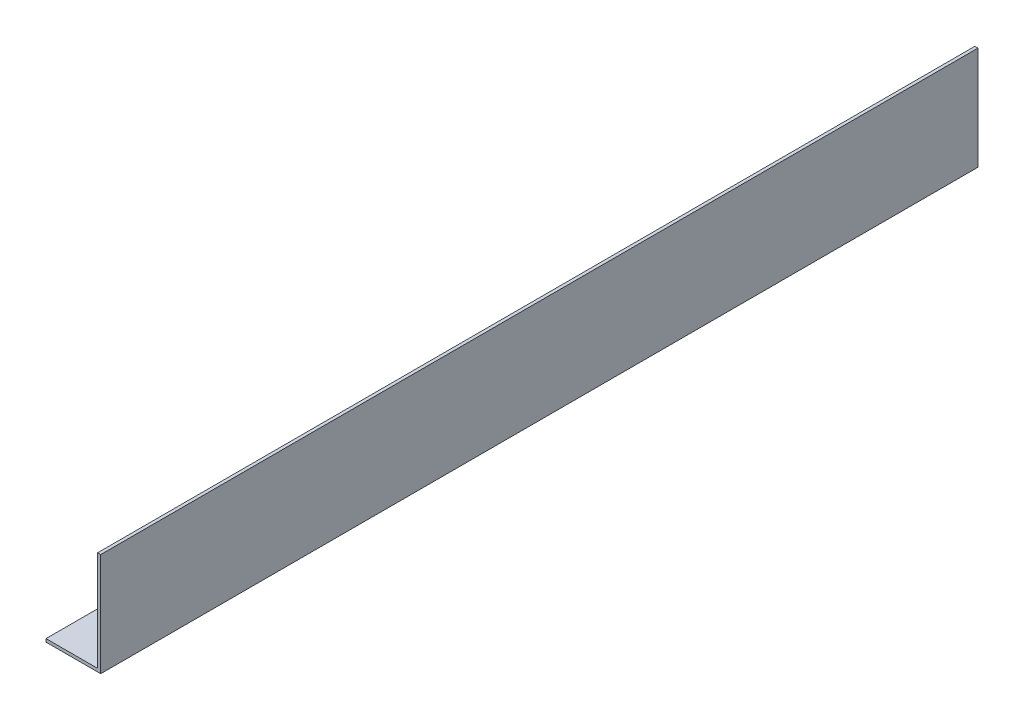
SolidWorks part; units mm, degrees
ref_plane "Front Plane" through (0, 0, 0) normal (0, 0, 1) x (1, 0, 0)
ref_plane "Top Plane" through (0, 0, 0) normal (0, 1, 0) x (1, 0, 0)
ref_plane "Right Plane" through (0, 0, 0) normal (1, 0, 0) x (0, 0, -1)
sketch "Sketch3" plane through (0, 0, 0) normal (0, 0, 1) x (1, 0, 0)
  line L11 (0, 0) -> (-26.924, 0)
  line L12 (0, 0) -> (0, 50.8)
  line L13 (0, 50.8) -> (-1.524, 50.8)
  line L14 (-1.524, 50.8) -> (-1.524, 1.524)
  line L15 (-1.524, 1.524) -> (-26.924, 1.524)
  line L16 (-26.924, 1.524) -> (-26.924, 0)
  dimension "D1" = 1.524
  dimension "D2" = 1.524
  dimension "D3" = 50.8
  dimension "D4" = 25.4
extrude "Boss-Extrude2" add sketch "Sketch3" along normal blind 431.8
sketch "Sketch4" plane through (0, 0, 0) normal (1, 0, 0) x (0, 0, -1)
  line L0 (-260.858, 26.162) -> (-384.048, 26.162) construction
  line L1 (-260.858, 11.557) -> (-384.048, 11.557)
  line L2 (-260.858, 40.767) -> (-384.048, 40.767)
  line L3 (-431.8, 0) -> (-431.8, 50.8) construction
  line L4 (-431.8, 50.8) -> (0, 50.8) construction
  arc A0 (-260.858, 11.557) -> (-260.858, 40.767) centre (-260.858, 26.162) ccw
  arc A1 (-384.048, 40.767) -> (-384.048, 11.557) centre (-384.048, 26.162) ccw
  point P2 (-322.453, 26.162)
  dimension "D1" = 47.752
  dimension "D4" = 123.19
  dimension "D2" = 29.21
  dimension "D3" = 24.638
